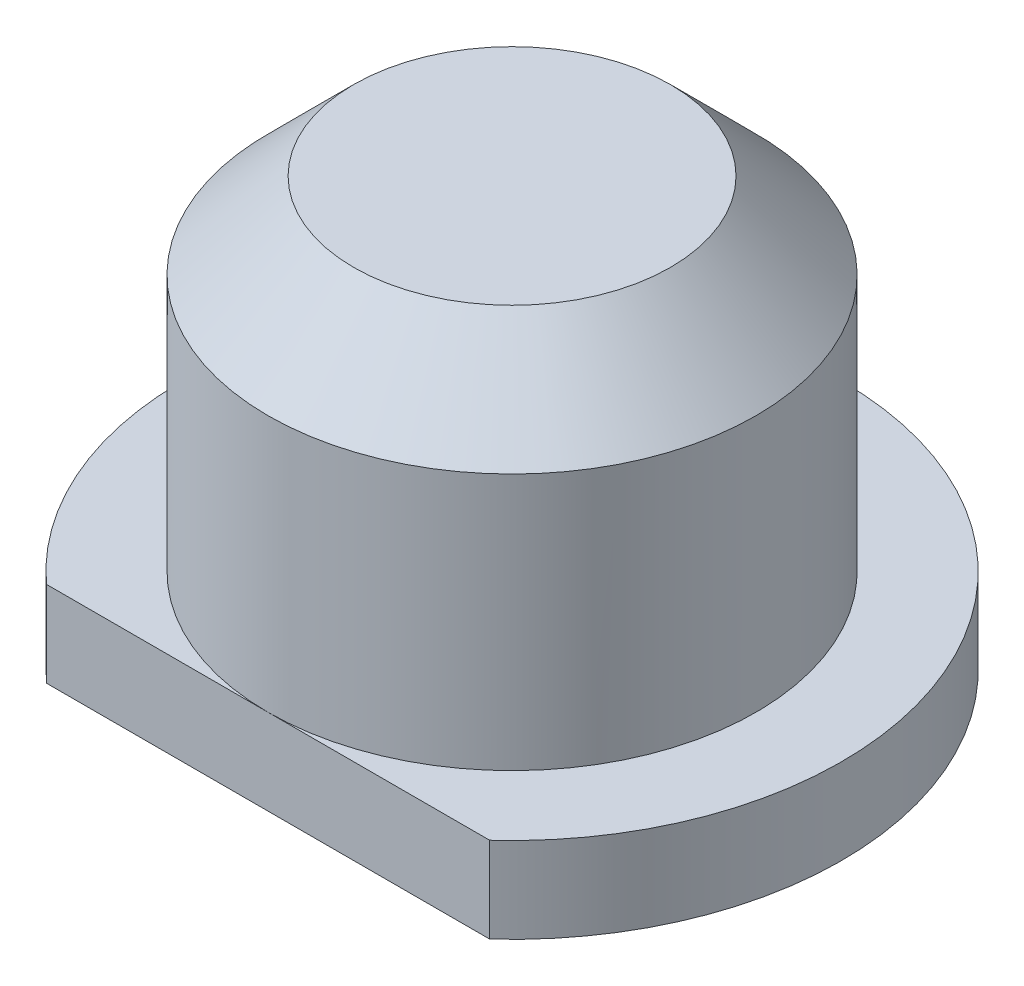
SolidWorks part; units mm, degrees
ref_plane "Front Plane" through (0, 0, 0) normal (0, 0, 1) x (1, 0, 0)
ref_plane "Top Plane" through (0, 0, 0) normal (0, 1, 0) x (1, 0, 0)
ref_plane "Right Plane" through (0, 0, 0) normal (1, 0, 0) x (0, 0, -1)
sketch "Sketch1" plane through (0, 0, 0) normal (0, 0, 1) x (1, 0, 0)
  line L0 (0, 3.5) -> (2, 3.5)
  line L1 (2, 3.5) -> (2, 0)
  line L2 (2, 0) -> (3.85, 0)
  line L3 (3.85, 0) -> (3.85, 1)
  line L4 (3.85, 1) -> (2.85, 1)
  line L5 (2.85, 1) -> (2.85, 5)
  line L6 (2.85, 5) -> (0, 5)
  line L7 (0, 5) -> (0, 3.5)
  line L8 (0, 3.5) -> (0, 0) construction
  dimension "D1" = 5.7
  dimension "D2" = 4
  dimension "D3" = 1
  dimension "D4" = 2.5
  dimension "D5" = 4
  dimension "D6" = 1
revolve "Revolve1" add sketch "Sketch1" angle 360 about L8
chamfer "Chamfer1" distance 1 angle 45 1 edges at (-2.85, 5, 0)
sketch "Sketch2" plane through (0, 1, 0) normal (0, 1, 0) x (1, 0, 0)
  line L1 (-2.5884, -2.85) -> (6.0382, -2.85)
  line L2 (-2.5884, -2.85) -> (-2.5884, -4.6366)
  line L3 (-2.5884, -4.6366) -> (6.0382, -4.6366)
  line L4 (6.0382, -2.85) -> (6.0382, -4.6366)
  circle A0 centre (0, 0) radius 3.85 construction
  circle A1 centre (0, 0) radius 2.85 construction
extrude "Cut-Extrude1" cut sketch "Sketch2" against normal through all
